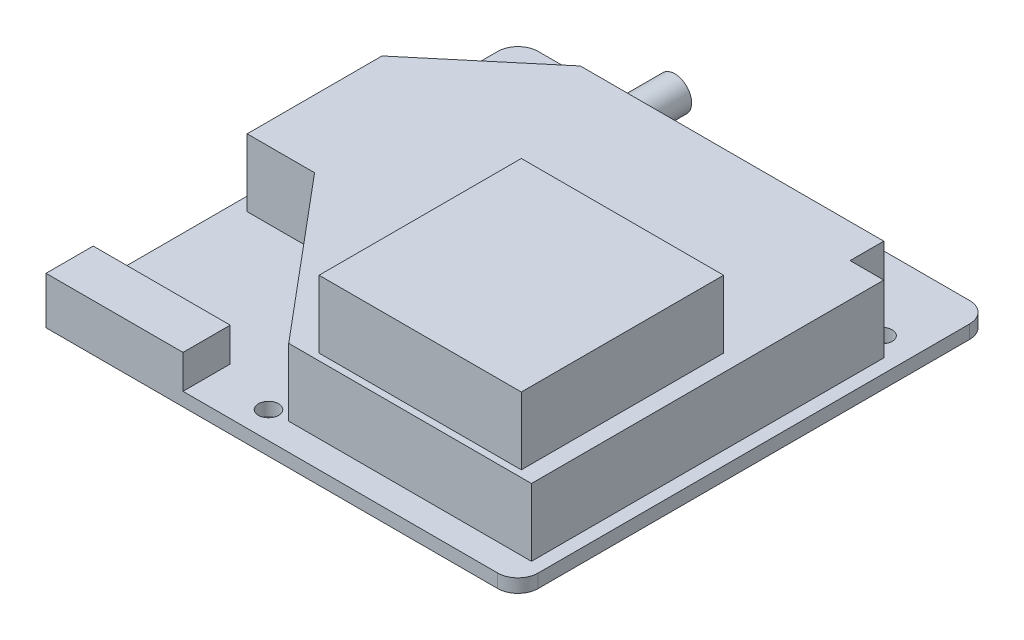
SolidWorks part; units mm, degrees
ref_plane "Ebene vorne" through (0, 0, 0) normal (0, 0, 1) x (1, 0, 0)
ref_plane "Ebene oben" through (0, 0, 0) normal (0, 1, 0) x (1, 0, 0)
ref_plane "Ebene rechts" through (0, 0, 0) normal (1, 0, 0) x (0, 0, -1)
sketch "Skizze1" plane through (0, 0, 0) normal (0, 1, 0) x (1, 0, 0)
  line L1 (-35, 35) -> (35, 35)
  line L2 (-35, 35) -> (-35, -35)
  line L3 (-35, -35) -> (35, -35)
  line L4 (35, 35) -> (35, -35)
  circle A0 centre (-6, -31) radius 1.5
  circle A1 centre (-30, 24) radius 1.5
  circle A2 centre (30, 24) radius 1.5
  point P4 (0, 35)
  point P6 (-35, 0)
  dimension "D5" = 3
  dimension "D6" = 3
  dimension "D8" = 3
  dimension "D1" = 70
  dimension "D2" = 70
  dimension "D3" = 5
  dimension "D4" = 11
  dimension "D7" = 60
  dimension "D9" = 41
  dimension "D10" = 55
extrude "Aufsatz-Linear austragen1" add sketch "Skizze1" along normal blind 2
sketch "Skizze2" plane through (0, 2, 0) normal (0, 1, 0) x (1, 0, 0)
  line L0 (-35, -35) -> (35, -35) construction
  line L1 (-35, -28) -> (-14.68, -28)
  line L2 (-35, -28) -> (-35, -35)
  line L3 (-35, -35) -> (-14.68, -35)
  line L4 (-14.68, -28) -> (-14.68, -35)
  line L5 (-35, 35) -> (-35, -35) construction
  dimension "D1" = 20.32
  dimension "D2" = 7
extrude "Aufsatz-Linear austragen2" add sketch "Skizze2" along normal blind 5
sketch "Skizze3" plane through (0, 2, 0) normal (0, 1, 0) x (1, 0, 0)
  line L0 (-33, -7.1649) -> (-23, -7.1649)
  line L1 (-23, -7.1649) -> (-3, -31)
  line L2 (-3, -31) -> (33, -31)
  line L3 (33, -31) -> (33, 21.2607)
  line L4 (33, 21.2607) -> (28, 21.2607)
  line L5 (28, 21.2607) -> (28, 26.2607)
  line L6 (28, 26.2607) -> (-17, 26.2607)
  line L7 (-17, 26.2607) -> (-33, 12.8351)
  line L8 (-33, 12.8351) -> (-33, -7.1649)
  line L9 (35, -35) -> (35, 35) construction
  line L10 (-35, 35) -> (-35, -28) construction
  circle A0 centre (-6, -31) radius 1.5 construction
  dimension "D1" = 10
  dimension "D2" = 20
  dimension "D3" = 130
  dimension "D4" = 45
  dimension "D5" = 5
  dimension "D6" = 5
  dimension "D7" = 2
  dimension "D8" = 2
  dimension "D9" = 3
extrude "Aufsatz-Linear austragen3" add sketch "Skizze3" along normal blind 10
sketch "Skizze4" plane through (0, 12, 0) normal (0, 1, 0) x (1, 0, 0)
  line L0 (33, -31) -> (33, 21.2607) construction
  line L1 (0.5, 0) -> (30.5, 0)
  line L2 (0.5, 0) -> (0.5, -30)
  line L3 (0.5, -30) -> (30.5, -30)
  line L4 (30.5, 0) -> (30.5, -30)
  line L5 (-3, -31) -> (33, -31) construction
  dimension "D1" = 30
  dimension "D2" = 30
  dimension "D3" = 2.5
  dimension "D4" = 1
extrude "Aufsatz-Linear austragen4" add sketch "Skizze4" along normal blind 10
sketch "Skizze5" plane through (0, 0, -26.2607) normal (0, 0, -1) x (-1, 0, 0)
  line L7 (-28, 2) -> (17, 2) construction
  line L8 (17, 12) -> (17, 2) construction
  circle A0 centre (13, 5.5) radius 2.5
  circle A1 centre (13, 5.5) radius 1.5
  dimension "D1" = 5
  dimension "D2" = 1
  dimension "D4" = 3
  dimension "D3" = 4
extrude "Aufsatz-Linear austragen5" add sketch "Skizze5" along normal blind 10
sketch "Skizze6" plane through (0, 0, 0) normal (0, -1, 0) x (1, 0, 0)
  line L0 (35, -35) -> (-35, -35) construction
  line L1 (-2, -25) -> (-27, -25)
  line L2 (-2, -25) -> (-2, 0)
  line L3 (-2, 0) -> (-27, 0)
  line L4 (-27, -25) -> (-27, 0)
  line L5 (-35, -35) -> (-35, 35) construction
  dimension "D1" = 10
  dimension "D2" = 8
  dimension "D3" = 25
  dimension "D4" = 25
extrude "Aufsatz-Linear austragen6" add sketch "Skizze6" along normal blind 3.5
fillet "Verrundung1" radius 3 3 edges at (35, 1, 35) (35, 1, -35) (-35, 1, -35)
